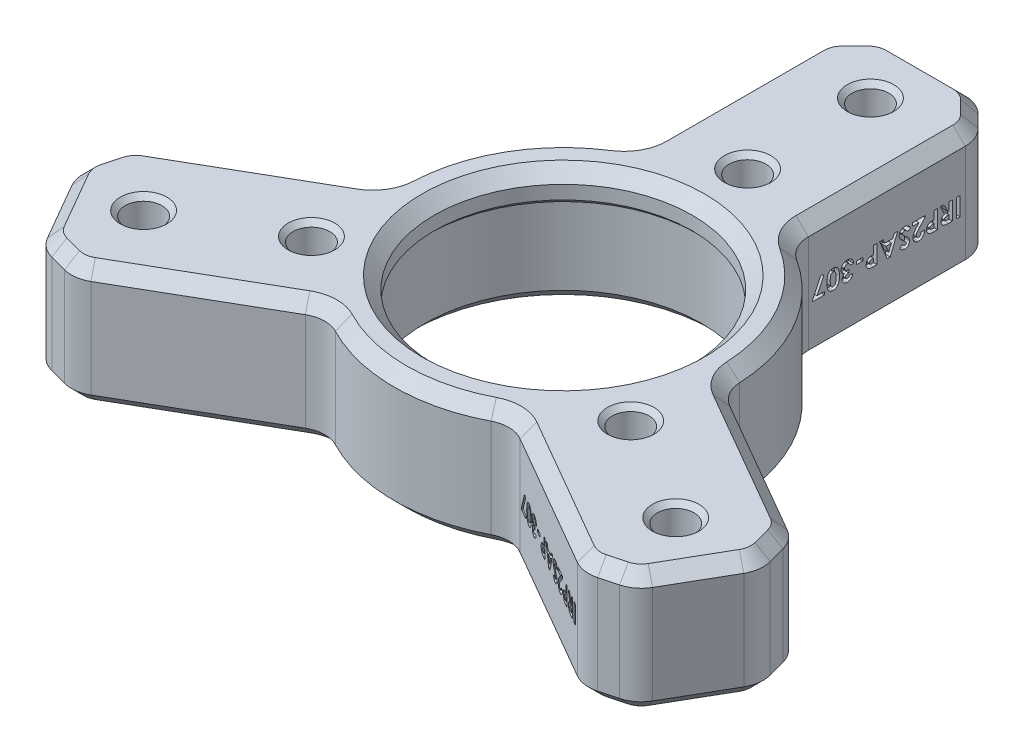
SolidWorks part; units mm, degrees
material "6061-T6 (SS)"
ref_plane "Front" through (0, 0, 0) normal (0, 0, 1) x (1, 0, 0)
ref_plane "Top" through (0, 0, 0) normal (0, 1, 0) x (1, 0, 0)
ref_plane "Right" through (0, 0, 0) normal (1, 0, 0) x (0, 0, -1)
sketch "Sketch1" plane through (0, 0, 0) normal (0, 1, 0) x (1, 0, 0)
  line L0 (-7.9375, 15.5543) -> (-7.9375, 38.1)
  line L1 (-7.9375, 38.1) -> (7.9375, 38.1)
  line L2 (7.9375, 38.1) -> (7.9375, 15.5543)
  line L3 (17.4391, -0.9031) -> (36.9643, -12.1759)
  line L4 (36.9643, -12.1759) -> (29.0268, -25.9241)
  line L5 (29.0268, -25.9241) -> (9.5016, -14.6512)
  line L6 (-9.5016, -14.6512) -> (-29.0268, -25.9241)
  line L7 (-29.0268, -25.9241) -> (-36.9643, -12.1759)
  line L8 (-36.9643, -12.1759) -> (-17.4391, -0.9031)
  line L9 (-32.9956, -19.05) -> (0, 0) construction
  line L10 (0, 0) -> (32.9956, -19.05) construction
  line L11 (0, 0) -> (0, 38.1) construction
  line L12 (7.9375, 38.1) -> (36.9643, -12.1759) construction
  line L13 (29.0268, -25.9241) -> (-29.0268, -25.9241) construction
  line L14 (-36.9643, -12.1759) -> (-7.9375, 38.1) construction
  circle A0 centre (0, 0) radius 13.335
  circle A1 centre (0, 0) radius 17.4625
  dimension "D1" = 26.67
  dimension "D2" = 34.925
  dimension "D3" = 15.875
  dimension "D4" = 38.1
extrude "Boss-Extrude1" add sketch "Sketch1" along normal blind 12.7 contours A1 L2 L1 L0 | A1 L8 L7 L6 | A1 L5 L4 L3 | A1 A0
chamfer "Chamfer1" distance 3.175 angle 45 6 edges at (-7.9375, 6.35, -38.1) (7.9375, 6.35, -38.1) (29.0268, 6.35, 25.9241) (36.9643, 6.35, 12.1759) (-36.9643, 6.35, 12.1759) (-29.0268, 6.35, 25.9241)
fillet "Fillet1" radius 3.175 18 edges at (17.4391, 6.35, 0.9031) (7.9375, 6.35, -15.5543) (-7.9375, 6.35, -15.5543) (-17.4391, 6.35, 0.9031) (9.5016, 6.35, 14.6512) (-9.5016, 6.35, 14.6512) (4.7625, 6.35, -38.1) (7.9375, 6.35, -34.925) (34.2147, 6.35, 10.5884) (35.3768, 6.35, 14.9256) (30.6143, 6.35, 23.1744) (-4.7625, 6.35, -38.1) (-7.9375, 6.35, -34.925) (26.2772, 6.35, 24.3366) (-34.2147, 6.35, 10.5884) (-35.3768, 6.35, 14.9256) (-30.6143, 6.35, 23.1744) (-26.2772, 6.35, 24.3366)
sketch "Sketch2" plane through (0, 0, 0) normal (0, -1, 0) x (1, 0, 0)
  circle A0 centre (0, 0) radius 14.2875
  dimension "D1" = 28.575
extrude "Cut-Extrude1" cut sketch "Sketch2" against normal blind 9.525
hole_wizard "#6 Clearance Hole1" positions "Sketch3" profile "Sketch4" hole size "#6" standard "ANSI Inch" end condition through all
sketch "Sketch3" plane through (0, 12.7, 0) normal (0, 1, 0) x (1, 0, 0)
  line L0 (0, 0) -> (-11.5484, -6.6675) construction
  line L1 (-11.5484, -6.6675) -> (-16.4978, -9.525) construction
  line L3 (-16.4978, -9.525) -> (-27.4963, -15.875) construction
  line L4 (-27.4963, -15.875) -> (-32.9956, -19.05) construction
  line L5 (-31.2719, -22.0355) -> (-34.7193, -16.0645) construction
  line L7 (0, 0) -> (0, 13.335) construction
  line L8 (0, 13.335) -> (0, 19.05) construction
  line L10 (0, 19.05) -> (0, 31.75) construction
  line L11 (0, 31.75) -> (0, 38.1) construction
  line L12 (-3.4474, 38.1) -> (3.4474, 38.1) construction
  line L14 (0, 0) -> (11.5484, -6.6675) construction
  line L15 (11.5484, -6.6675) -> (16.4978, -9.525) construction
  line L17 (16.4978, -9.525) -> (27.4963, -15.875) construction
  line L18 (27.4963, -15.875) -> (32.9956, -19.05) construction
  line L19 (34.7193, -16.0645) -> (31.2719, -22.0355) construction
  circle A0 centre (0, 0) radius 13.335 construction
  point P0 (-27.4963, -15.875)
  point P2 (-16.4978, -9.525)
  point P4 (0, 19.05)
  point P6 (0, 31.75)
  point P8 (16.4978, -9.525)
  point P10 (27.4963, -15.875)
  dimension "D1" = 12.7
  dimension "D2" = 19.05
sketch "Sketch4" plane through (-27.4963, 12.7, 15.875) normal (1, 0, 0) x (0, 0, 1)
  line L0 (0, 0) -> (0, 12.7)
  line L1 (0, 12.7) -> (1.8986, 12.7)
  line L2 (1.8986, 12.7) -> (1.8986, 0)
  line L5 (1.8986, 0) -> (0, 0)
  line L11 (0, -6.35) -> (0, 107.95) construction
  dimension "Thru Hole Dia." = 3.7973
  dimension "Thru Hole Depth" = 12.7
chamfer "Chamfer2" distance 0.508 angle 45 13 edges at (0, 0, -29.8514) (0, 12.7, -29.8514) (0, 0, -17.1514) (0, 12.7, -17.1514) (27.4963, 0, 17.7736) (27.4963, 12.7, 17.7736) (16.4978, 0, 11.4236) (16.4978, 12.7, 11.4236) (-16.4978, 0, 11.4236) (-16.4978, 12.7, 11.4236) (-27.4963, 0, 17.7736) (-27.4963, 12.7, 17.7736) (0, 9.525, -13.335)
chamfer "Chamfer3" distance 1.27 angle 45 74 edges at (0, 12.7, 13.335) (0, 0, -14.2875) (-6.35, 12.7, -36.5125) (-6.35, 0, -36.5125) (-4.6624, 0, -37.8583) (-4.6624, 12.7, -37.8583) (-7.6958, 12.7, -34.8249) (-7.6958, 0, -34.8249) (0, 12.7, -38.1) (0, 0, -38.1) (-7.9375, 12.7, -25.5) (-7.9375, 0, -25.5) (4.6624, 12.7, -37.8583) (4.6624, 0, -37.8583) (-8.3278, 12.7, -15.865) (-8.3278, 0, -15.865) (6.35, 0, -36.5125) (6.35, 12.7, -36.5125) (-15.123, 12.7, -8.7313) (-15.123, 0, -8.7313) (7.6958, 0, -34.8249) (7.6958, 12.7, -34.8249) (-17.9034, 12.7, 0.7204) (-17.9034, 0, 0.7204) (7.9375, 0, -25.5) (7.9375, 12.7, -25.5) (-26.0524, 0, 5.8759) (-26.0524, 12.7, 5.8759) (8.3278, 12.7, -15.865) (8.3278, 0, -15.865) (-34.0071, 0, 10.7477) (-34.0071, 12.7, 10.7477) (15.123, 12.7, -8.7312) (15.123, 0, -8.7312) (-34.7958, 12.7, 12.757) (-34.7958, 0, 12.757) (17.9034, 12.7, 0.7204) (17.9034, 0, 0.7204) (-35.1175, 12.7, 14.8914) (-35.1175, 0, 14.8914) (26.0524, 12.7, 5.8759) (26.0524, 0, 5.8759) (-32.9956, 12.7, 19.05) (-32.9956, 0, 19.05) (34.0071, 12.7, 10.7477) (34.0071, 0, 10.7477) (-30.4551, 0, 22.9669) (-30.4551, 12.7, 22.9669) (34.7958, 0, 12.757) (34.7958, 12.7, 12.757) (-28.4458, 12.7, 23.7555) (-28.4458, 0, 23.7555) (35.1175, 0, 14.8914) (35.1175, 12.7, 14.8914) (-26.3113, 12.7, 24.0772) (-26.3113, 0, 24.0772) (32.9956, 0, 19.05) (32.9956, 12.7, 19.05) (-18.1149, 12.7, 19.6241) (-18.1149, 0, 19.6241) (30.4551, 12.7, 22.9669) (30.4551, 0, 22.9669) (-9.5755, 12.7, 15.1446) (-9.5755, 0, 15.1446) (28.4458, 0, 23.7555) (28.4458, 12.7, 23.7555) (0, 0, 17.4625) (0, 12.7, 17.4625) (26.3113, 0, 24.0772) (26.3113, 12.7, 24.0772) (9.5755, 12.7, 15.1446) (9.5755, 0, 15.1446) (18.1149, 0, 19.6241) (18.1149, 12.7, 19.6241)
sketch "Sketch5" plane through (7.9375, 0, 0) normal (1, 0, 0) x (0, 0, -1)
  line L0 (33.6099, 7.3025) -> (17.3902, 7.3025) construction
  line L1 (33.6099, 1.27) -> (33.6099, 11.43) construction
  line L2 (17.3902, 11.43) -> (17.3902, 1.27) construction
  line L3 (25.5, 1.27) -> (25.5, 5.3975) construction
  line L4 (17.3902, 1.27) -> (33.6099, 1.27) construction
  line L5 (25.5, 5.3975) -> (25.5, 7.3025) construction
  line L6 (25.5, 7.3025) -> (25.5, 11.43) construction
  line L7 (33.6099, 11.43) -> (17.3902, 11.43) construction
  text T0 "<b>IRP2SAP-307</b>" font "Century Gothic" height 1.905
  dimension "D1" = 1.905
extrude "Cut-Extrude2" cut sketch "Sketch5" against normal blind 0.508
sketch "Sketch6" plane through (-3.9688, 0, 6.8741) normal (-0.5, 0, 0.866) x (0.866, 0, 0.5)
  line L0 (25.5, 1.27) -> (25.5, 5.3975) construction
  line L1 (17.3902, 1.27) -> (33.6099, 1.27) construction
  line L2 (25.5, 5.3975) -> (25.5, 7.3025) construction
  line L3 (25.5, 7.3025) -> (25.5, 11.43) construction
  line L4 (33.6099, 11.43) -> (17.3902, 11.43) construction
  line L5 (33.6099, 7.3025) -> (17.3902, 7.3025) construction
  line L6 (33.6099, 1.27) -> (33.6099, 11.43) construction
  line L7 (17.3902, 11.43) -> (17.3902, 1.27) construction
  text T0 "<b>IRP2SAP-307</b>" font "Century Gothic" height 1.905
  dimension "D1" = 1.905
extrude "Cut-Extrude3" cut sketch "Sketch6" against normal blind 0.508
sketch "Sketch7" plane through (-3.9688, 0, -6.8741) normal (-0.5, 0, -0.866) x (-0.866, 0, 0.5)
  line L0 (33.6099, 7.3025) -> (17.3902, 7.3025) construction
  line L1 (33.6099, 1.27) -> (33.6099, 11.43) construction
  line L2 (17.3902, 11.43) -> (17.3902, 1.27) construction
  line L3 (25.5, 11.43) -> (25.5, 7.3025) construction
  line L4 (33.6099, 11.43) -> (17.3902, 11.43) construction
  line L5 (25.5, 7.3025) -> (25.5, 5.3975) construction
  line L6 (25.5, 5.3975) -> (25.5, 1.27) construction
  line L7 (17.3902, 1.27) -> (33.6099, 1.27) construction
  text T0 "<b>IRP2SAP-307</b>" font "Century Gothic" height 1.905
  dimension "D1" = 1.905
extrude "Cut-Extrude4" cut sketch "Sketch7" against normal blind 0.508
